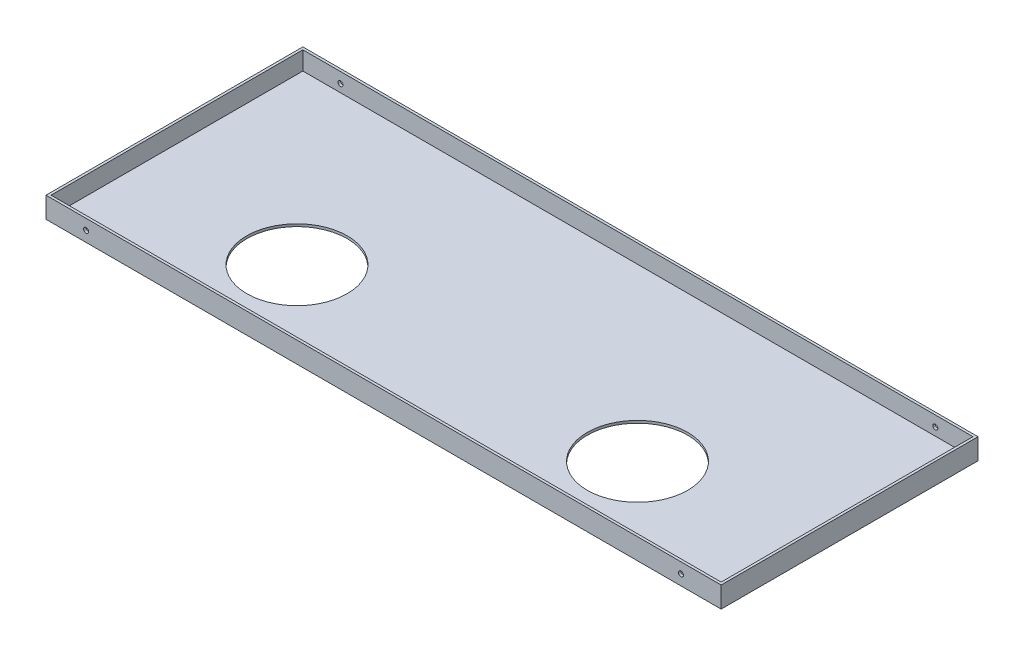
SolidWorks part; units mm, degrees
ref_plane "前基準面" through (0, 0, 0) normal (0, 0, 1) x (1, 0, 0)
ref_plane "上基準面" through (0, 0, 0) normal (0, 1, 0) x (1, 0, 0)
ref_plane "右基準面" through (0, 0, 0) normal (1, 0, 0) x (0, 0, -1)
sketch "草圖2" plane through (0, 0, 0) normal (0, 1, 0) x (1, 0, 0)
  line L0 (0, 0) -> (0, -307)
  line L1 (0, -307) -> (807, -307)
  line L2 (807, -307) -> (807, 0)
  line L3 (807, 0) -> (0, 0)
  dimension "D1" = 807
  dimension "D2" = 307
extrude "填料-伸長1" add sketch "草圖2" along normal blind 25
sketch "草圖3" plane through (0, 25, 0) normal (0, 1, 0) x (1, 0, 0)
  line L14 (804, -304) -> (804, -3)
  line L15 (3, -304) -> (804, -304)
  line L16 (3, -3) -> (3, -304)
  line L17 (804, -3) -> (3, -3)
  line L18 (804, -304) -> (804, -3)
  line L19 (3, -304) -> (804, -304)
  line L20 (3, -3) -> (3, -304)
  line L21 (804, -3) -> (3, -3)
  dimension "D1" = 3
extrude "除料-伸長1" cut sketch "草圖3" against normal blind 22
sketch "草圖4" plane through (0, 0, 307) normal (0, 0, 1) x (1, 0, 0)
  line L0 (807, 25) -> (807, 0) construction
  line L1 (0, 25) -> (807, 25) construction
  line L2 (0, 25) -> (0, 0) construction
  circle A0 centre (759, 12.5) radius 3
  circle A1 centre (48, 12.5) radius 3
  dimension "D1" = 6
  dimension "D4" = 6
  dimension "D2" = 48
  dimension "D3" = 12.5
  dimension "D5" = 48
  dimension "D6" = 12.5
extrude "除料-伸長2" cut sketch "草圖4" against normal through all
sketch "草圖5" plane through (0, 0, 0) normal (0, -1, 0) x (1, 0, 0)
  line L1 (0, 307) -> (807, 307) construction
  line L2 (807, 307) -> (807, 0) construction
  line L3 (0, 0) -> (0, 307) construction
  circle A0 centre (607, 207) radius 60
  circle A1 centre (200, 207) radius 60
  dimension "D1" = 120
  dimension "D3" = 120
  dimension "D2" = 100
  dimension "D4" = 100
  dimension "D5" = 200
  dimension "D6" = 200
extrude "除料-伸長3" cut sketch "草圖5" against normal through all
